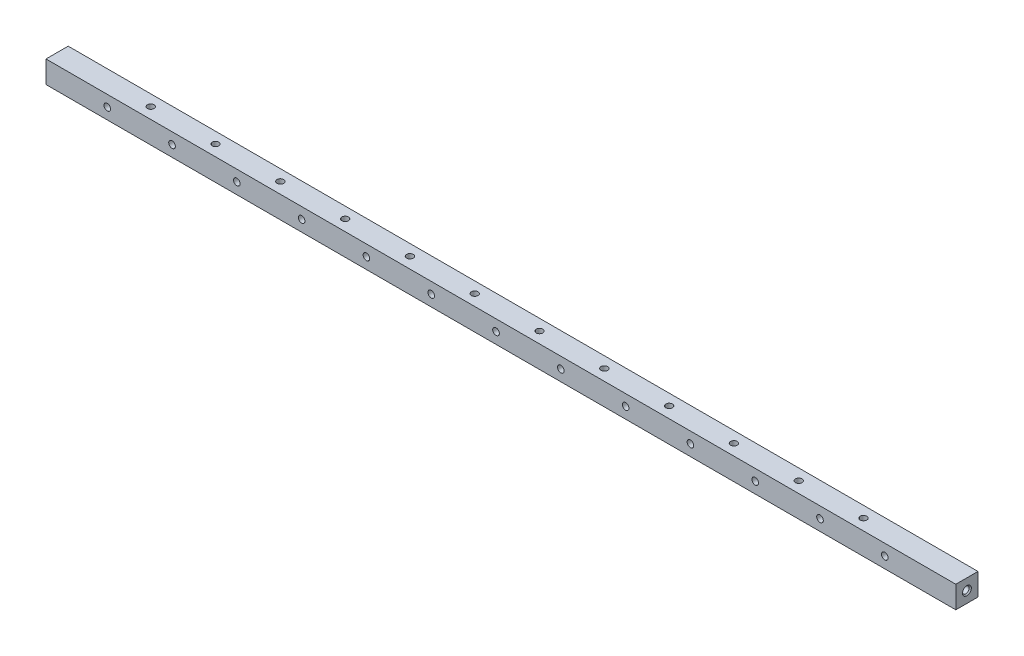
SolidWorks part; units mm, degrees
material "6061 Alloy"
ref_plane "Front Plane" through (0, 0, 0) normal (0, 0, 1) x (1, 0, 0)
ref_plane "Top Plane" through (0, 0, 0) normal (0, 1, 0) x (1, 0, 0)
ref_plane "Right Plane" through (0, 0, 0) normal (1, 0, 0) x (0, 0, -1)
sketch "Sketch1" plane through (0, 0, 0) normal (1, 0, 0) x (0, 0, -1)
  line L1 (6.35, -6.35) -> (-6.35, -6.35)
  line L2 (6.35, -6.35) -> (6.35, 6.35)
  line L3 (6.35, 6.35) -> (-6.35, 6.35)
  line L4 (-6.35, -6.35) -> (-6.35, 6.35)
  line L5 (6.35, -6.35) -> (-6.35, 6.35) construction
  line L6 (6.35, 6.35) -> (-6.35, -6.35) construction
  point P0 (0, 0)
  dimension "D1" = 12.7
  dimension "D2" = 12.7
extrude "Boss-Extrude1" add sketch "Sketch1" along normal blind 520.7
sketch "Sketch2" plane through (0, 0, 0) normal (-1, 0, 0) x (0, 0, 1)
  circle A0 centre (0, 0) radius 4.7625
  dimension "D1" = 9.525
sketch "Sketch9" plane through (520.7, 0, 0) normal (1, 0, 0) x (0, 0, -1)
  circle A0 centre (0, 0) radius 4.7625
  dimension "D1" = 9.525
hole_wizard "#10-24 Tapped Hole1" positions "Sketch12" profile "Sketch13" tap size "#10-24" standard "ANSI Inch" end condition through all
sketch "Sketch12" plane through (0, 0, 6.35) normal (0, 0, 1) x (1, 0, 0)
  line L0 (0, 6.35) -> (0, -6.35) construction
  point P0 (35.052, 0)
  dimension "D1" = 35.052
sketch "Sketch13" plane through (35.052, 0, 6.35) normal (1, 0, 0) x (0, -1, 0)
  line L0 (0, 0) -> (0, 12.7)
  line L1 (0, 12.7) -> (1.8986, 12.7)
  line L2 (1.8986, 12.7) -> (1.8986, 0)
  line L5 (1.8986, 0) -> (0, 0)
  line L11 (0, -6.35) -> (0, 107.95) construction
  dimension "Thru Tap Drill Dia." = 3.7973
  dimension "Thru Tap Drill Depth" = 12.7
cosmetic thread "Hole Thread1" parameters "D2"=4.826
hole_wizard "#10-24 Tapped Hole2" positions "Sketch14" profile "Sketch15" tap size "#10-24" standard "ANSI Inch" end condition through all
sketch "Sketch14" plane through (0, 6.35, 0) normal (0, 1, 0) x (1, 0, 0)
  line L0 (0, 6.35) -> (0, -6.35) construction
  point P0 (53.594, 0)
  dimension "D1" = 53.594
sketch "Sketch15" plane through (53.594, 6.35, 0) normal (1, 0, 0) x (0, 0, 1)
  line L0 (0, 0) -> (0, 12.7)
  line L1 (0, 12.7) -> (1.8986, 12.7)
  line L2 (1.8986, 12.7) -> (1.8986, 0)
  line L5 (1.8986, 0) -> (0, 0)
  line L11 (0, -6.35) -> (0, 107.95) construction
  dimension "Thru Tap Drill Dia." = 3.7973
  dimension "Thru Tap Drill Depth" = 12.7
cosmetic thread "Hole Thread2" parameters "D2"=4.826
hole_wizard "M6x1.0 Tapped Hole2" positions "Sketch18" profile "Sketch19" tap size "M6x1.0" standard "ANSI Metric"
sketch "Sketch18" plane through (0, 0, 0) normal (-1, 0, 0) x (0, 0, 1)
  point P0 (0, 0)
sketch "Sketch19" plane through (0, 0, 0) normal (0, 1, 0) x (0, 0, 1)
  line L0 (0, 0) -> (0, 21.8222)
  line L1 (0, 21.8222) -> (2.5, 20.32)
  line L2 (2.5, 20.32) -> (2.5, 0.525)
  line L3 (2.5, 0.525) -> (3.025, 0)
  line L5 (3.025, 0) -> (0, 0)
  line L6 (-2.5, 0.525) -> (-3.025, 0) construction
  line L10 (0, 21.8222) -> (-2.5, 20.32) construction
  line L11 (0, -6.35) -> (0, 107.95) construction
  dimension "Tap Drill Dia." = 5
  dimension "Tap Drill Depth" = 20.32
  dimension "Near C'Sink Dia." = 6.05
  dimension "Near C'Sink Angle" = 90
  dimension "Drill Angle" = 118
cosmetic thread "Hole Thread6" parameters "D1"=15.24, "D2"=6
hole_wizard "#10-24 Tapped Hole3" positions "Sketch20" profile "Sketch21" tap size "#10-24" standard "ANSI Inch"
sketch "Sketch20" plane through (520.7, 0, 0) normal (1, 0, 0) x (0, 0, -1)
  point P0 (0, 0)
sketch "Sketch21" plane through (520.7, 0, 0) normal (0, 1, 0) x (0, 0, -1)
  line L0 (0, 0) -> (0, 21.7148)
  line L1 (0, 21.7148) -> (1.8986, 20.574)
  line L2 (1.8986, 20.574) -> (1.8986, 0.635)
  line L3 (1.8986, 0.635) -> (2.5337, 0)
  line L5 (2.5337, 0) -> (0, 0)
  line L6 (-1.8986, 0.635) -> (-2.5337, 0) construction
  line L10 (0, 21.7148) -> (-1.8987, 20.574) construction
  line L11 (0, -6.35) -> (0, 107.95) construction
  dimension "Tap Drill Dia." = 3.7973
  dimension "Tap Drill Depth" = 20.574
  dimension "Near C'Sink Dia." = 5.0673
  dimension "Near C'Sink Angle" = 90
  dimension "Drill Angle" = 118
cosmetic thread "Hole Thread9" parameters "D1"=15.24, "D2"=6
pattern_linear "LPattern1" count 13 spacing 37.084 along (1, 0, 0) of "#10-24 Tapped Hole1"
pattern_linear "LPattern2" count 12 spacing 37.084 along (1, 0, 0) of "#10-24 Tapped Hole2"
